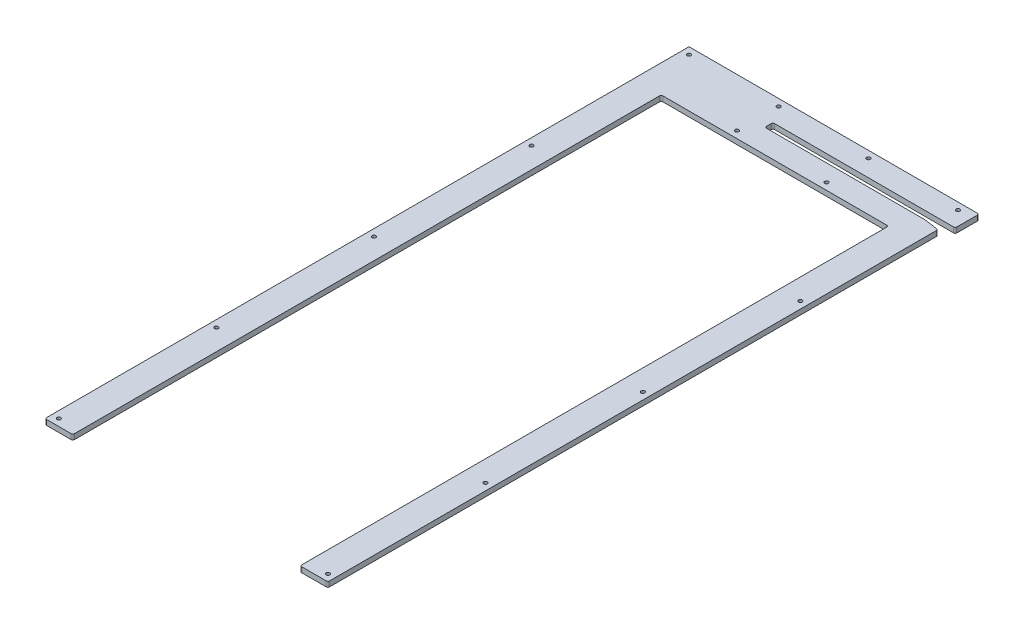
SolidWorks part; units mm, degrees
material "PE Low/Medium Density"
ref_plane "Front Plane" through (0, 0, 0) normal (0, 0, 1) x (1, 0, 0)
ref_plane "Top Plane" through (0, 0, 0) normal (0, 1, 0) x (1, 0, 0)
ref_plane "Right Plane" through (0, 0, 0) normal (1, 0, 0) x (0, 0, -1)
sketch "Sketch1" plane through (0, 0, 0) normal (0, 1, 0) x (1, 0, 0)
  line L0 (-258.3, 0) -> (-207.5, 0)
  line L1 (-207.5, 0) -> (-207.5, 1074.4)
  line L2 (-207.5, 1074.4) -> (207.5, 1074.4)
  line L3 (207.5, 1074.4) -> (207.5, 0)
  line L4 (207.5, 0) -> (258.3, 0)
  line L5 (258.3, 0) -> (258.3, 1113.9149)
  line L6 (230.3, 1117.85) -> (-61.7, 1117.85)
  line L7 (-61.7, 1117.85) -> (-61.7, 1132.55)
  line L8 (-61.7, 1132.55) -> (271.3, 1132.55)
  line L9 (271.3, 1132.55) -> (271.3, 1176)
  line L10 (271.3, 1176) -> (-258.3, 1176)
  line L11 (-258.3, 1176) -> (-258.3, 0)
  line L12 (-207.5, 0) -> (207.5, 0) construction
  line L13 (-182.147, 1176) -> (-182.147, 1074.4) construction
  line L14 (-61.7, 1125.2) -> (-162.228, 1125.2) construction
  line L15 (230.3, 1117.85) -> (258.3, 1113.9149)
  point P0 (0, 0)
  point P18 (-182.147, 1125.2)
  dimension "D1" = 516.6
  dimension "D2" = 1176
  dimension "D3" = 50.8
  dimension "D4" = 101.6
  dimension "D5" = 14.7
  dimension "D6" = 320
  dimension "D7" = 13
  dimension "D8" = 8
  dimension "D9" = 28
extrude "Boss-Extrude1" add sketch "Sketch1" along normal blind 9.525
sketch "Sketch4" [suppressed] plane through (0, 0, 0) normal (0, -1, 0) x (1, 0, 0)
  line L0 (271.3, -1277.6) -> (-258.3, -1277.6) construction
  line L1 (-258.3, -1277.6) -> (-207.5, -1277.6)
  line L2 (-258.3, -1277.6) -> (-258.3, -1477.6)
  line L3 (-258.3, -1477.6) -> (-207.5, -1477.6)
  line L4 (-207.5, -1277.6) -> (-207.5, -1477.6)
  line L5 (258.3, -1277.6) -> (207.5, -1277.6)
  line L6 (258.3, -1277.6) -> (258.3, -1477.6)
  line L7 (258.3, -1477.6) -> (207.5, -1477.6)
  line L8 (207.5, -1277.6) -> (207.5, -1477.6)
  line L9 (258.3, 0) -> (258.3, -1215.5149) construction
  line L10 (207.5, -1176) -> (207.5, 0) construction
  line L11 (-207.5, 0) -> (-207.5, -1176) construction
  dimension "D1" = 200
extrude "Boss-Extrude2" [suppressed] add sketch "Sketch4" against normal up to surface (9.525 mm away)
hole_wizard "CSK for 1/4 Flat Head Machine Screw (100)1" positions "Sketch3" profile "Sketch2" countersink size "1/4" standard "Ansi Inch" end condition through all
sketch "Sketch3" plane through (0, 0, 0) normal (0, -1, 0) x (1, 0, 0)
  line L0 (271.3, -1176) -> (-258.3, -1176) construction
  line L1 (-258.3, -1176) -> (-258.3, 0) construction
  point P0 (-245.6, -1163.3)
  dimension "D1" = 12.7
  dimension "D2" = 12.7
sketch "Sketch2" plane through (-245.6, 0, -1163.3) normal (1, 0, 0) x (0, 0, -1)
  line L0 (0, 0) -> (0, 9.525)
  line L1 (0, 9.525) -> (3.3782, 9.525)
  line L2 (3.3782, 9.525) -> (3.3782, 4.5682)
  line L3 (3.3782, 4.5682) -> (8.8224, 0)
  line L5 (8.8224, 0) -> (0, 0)
  line L6 (-3.3782, 4.5682) -> (-8.8224, 0) construction
  line L11 (0, -6.35) -> (0, 107.95) construction
  dimension "Thru Hole Dia." = 6.7564
  dimension "Thru Hole Depth" = 9.525
  dimension "Near C'Sink Dia." = 17.6448
  dimension "Near C'Sink Angle" = 100
pattern_linear "LPattern1" count 2 spacing 491.2 along (1, 0, 0) count 5 spacing 287.65 along (0, 0, 1) of "CSK for 1/4 Flat Head Machine Screw (100)1"
pattern_linear "LPattern3" [suppressed] count 2 spacing 491.2 count 5 spacing 313.05
pattern_linear "LPattern2" count 3 spacing 163.7333 along (1, 0, 0) count 2 spacing 76.2 along (0, 0, 1) skipping (0, 1) of "CSK for 1/4 Flat Head Machine Screw (100)1"
hole_wizard "CSK for 1/4 Flat Head Machine Screw (100)2" positions "Sketch6" profile "Sketch5" countersink size "1/4" standard "Ansi Inch"
sketch "Sketch6" plane through (0, 0, 0) normal (0, -1, 0) x (1, 0, 0)
  line L0 (-258.3, -1477.6) -> (-207.5, -1477.6) construction
  line L1 (-258.3, -1477.6) -> (-258.3, 0) construction
  point P0 (-245.6, -1464.9)
  dimension "D1" = 12.7
  dimension "D2" = 12.7
sketch "Sketch5" plane through (-245.6, 0, -1464.9) normal (1, 0, 0) x (0, 0, -1)
  line L0 (0, 0) -> (0, 9.525)
  line L1 (0, 9.525) -> (3.3782, 9.525)
  line L2 (3.3782, 9.525) -> (3.3782, 4.5682)
  line L3 (3.3782, 4.5682) -> (8.8224, 0)
  line L5 (8.8224, 0) -> (0, 0)
  line L6 (-3.3782, 4.5682) -> (-8.8224, 0) construction
  line L11 (0, -6.35) -> (0, 107.95) construction
  dimension "Thru Hole Dia." = 6.7564
  dimension "Thru Hole Depth" = 9.5251
  dimension "Near C'Sink Dia." = 17.6448
  dimension "Near C'Sink Angle" = 100
mirror "Mirror1" [suppressed] about plane through (0, 0, 0) normal (1, 0, 0)
fillet "Fillet1" radius 3.175 11 edges at (258.3, 4.7625, 0) (207.5, 4.7625, 0) (-207.5, 4.7625, 0) (-258.3, 4.7625, 0) (207.5, 4.7625, -1074.4) (-207.5, 4.7625, -1074.4) (258.3, 4.7625, -1113.9149) (271.3, 4.7625, -1132.55) (271.3, 4.7625, -1176) (-61.7, 4.7625, -1117.85) (-61.7, 4.7625, -1132.55)
fillet "Fillet2" [suppressed] radius 3.175
move or copy body "Body-Move/Copy1" [suppressed] bodies to move or copy 110
move or copy body "Body-Move/Copy2" [suppressed] bodies to move or copy 113
